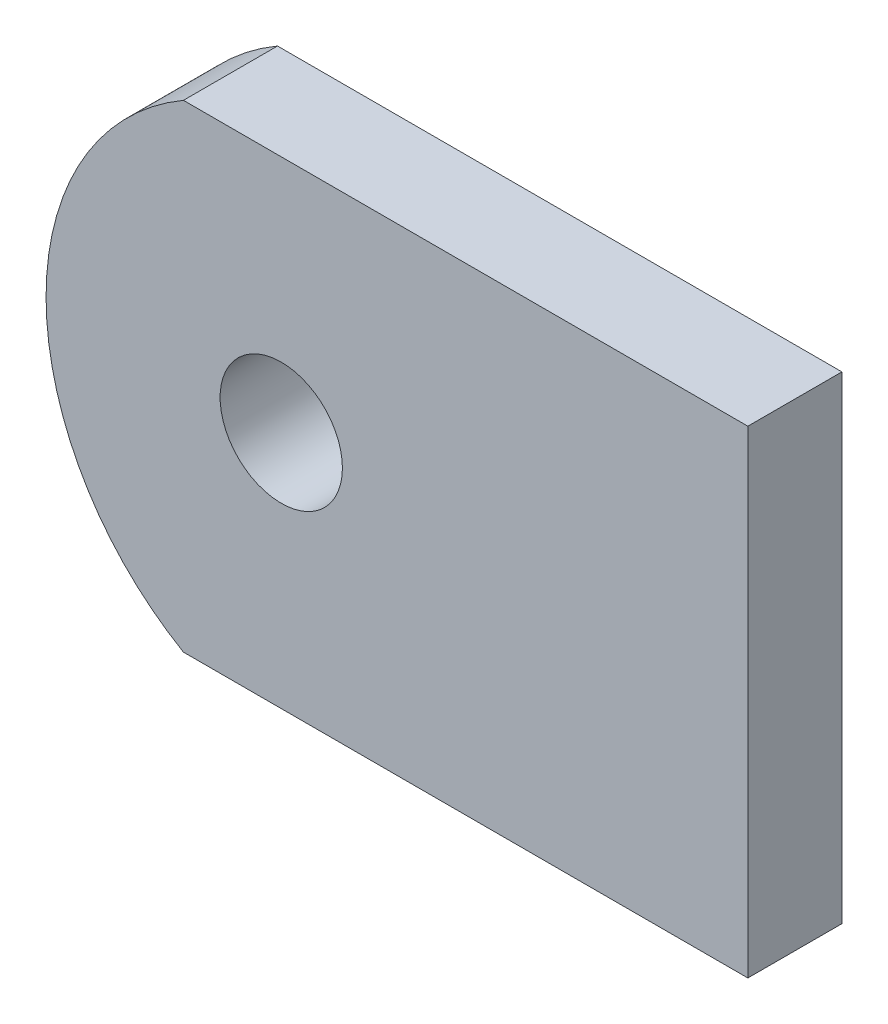
SolidWorks part; units mm, degrees
ref_plane "Front Plane" through (0, 0, 0) normal (0, 0, 1) x (1, 0, 0)
ref_plane "Top Plane" through (0, 0, 0) normal (0, 1, 0) x (1, 0, 0)
ref_plane "Right Plane" through (0, 0, 0) normal (1, 0, 0) x (0, 0, -1)
sketch "Sketch2" plane through (-6.4667, 0, 0) normal (0, 0, 1) x (1, 0, 0)
  line L0 (-251, 269.6842) -> (-251, 190.213) construction
  line L1 (-251, 239.4585) -> (-281, 239.4585)
  line L2 (-251, 239.4585) -> (-251, 214.0585)
  line L3 (-251, 214.0585) -> (-281, 214.0585)
  arc A0 (-281, 239.4585) -> (-281, 214.0585) centre (-273.6027, 226.7585) ccw
  circle A1 centre (-275.8, 226.7585) radius 3.25
  point P1 (-288.3, 226.7585)
  point P6 (-281, 239.4585)
  point P8 (-281, 214.0585)
  point P13 (0, 0)
  dimension "D5" = 12.7
  dimension "D3" = 12.5
  dimension "D6" = 6.5
  dimension "D1" = 25.4
  dimension "D2" = 37.3
  dimension "D4" = 30
extrude "Boss-Extrude1" add sketch "Sketch2" along normal blind 5
